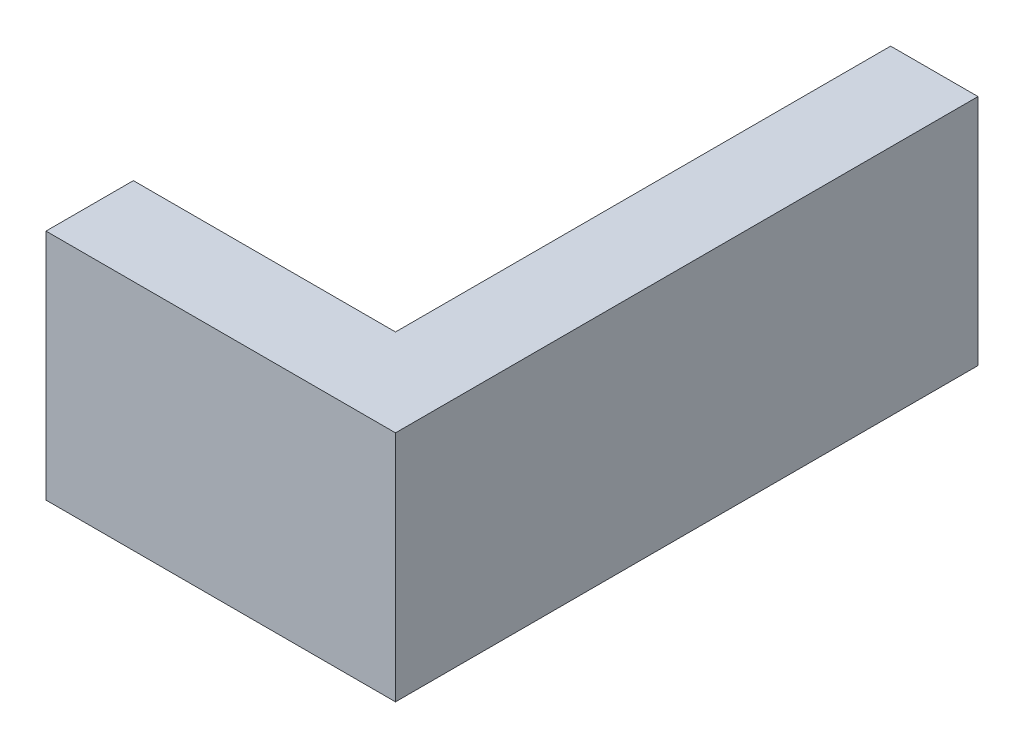
SolidWorks part; units mm, degrees
ref_plane "Front" through (0, 0, 0) normal (0, 0, 1) x (1, 0, 0)
ref_plane "Top" through (0, 0, 0) normal (0, 1, 0) x (1, 0, 0)
ref_plane "Right" through (0, 0, 0) normal (1, 0, 0) x (0, 0, -1)
sketch "Sketch1" plane through (0, 0, 0) normal (0, 1, 0) x (1, 0, 0)
  line L1 (0, 0) -> (76.2, 0)
  line L2 (0, 0) -> (0, 19.05)
  line L3 (0, 19.05) -> (76.2, 19.05)
  line L4 (76.2, 0) -> (76.2, 19.05)
  line L5 (76.2, 19.05) -> (57.15, 19.05)
  line L6 (76.2, 19.05) -> (76.2, 127)
  line L7 (76.2, 127) -> (57.15, 127)
  line L8 (57.15, 19.05) -> (57.15, 127)
  dimension "D1" = 19.05
  dimension "D2" = 127
  dimension "D3" = 76.2
extrude "Boss-Extrude1" add sketch "Sketch1" along normal mid plane 50.8 contours L8 L3 L6 L7 | L1 L4 L3 L2
